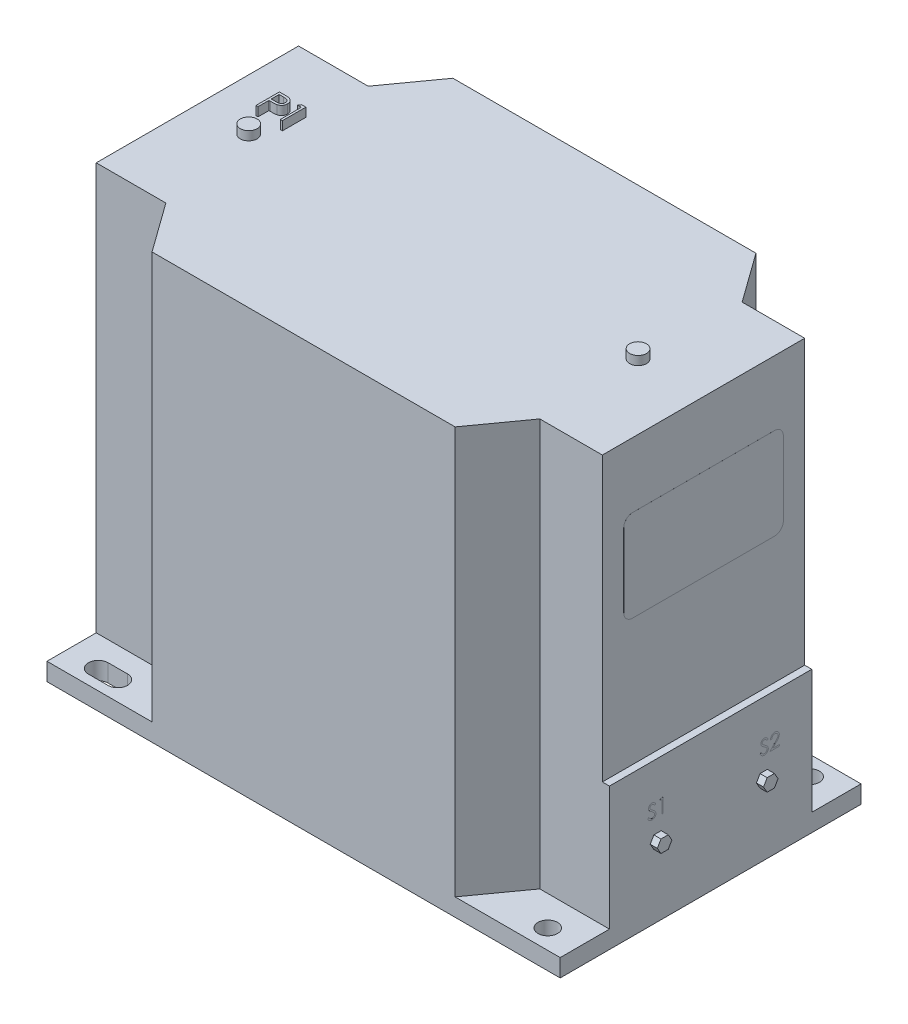
SolidWorks part; units mm, degrees
ref_plane "Alzado" through (0, 0, 0) normal (0, 0, 1) x (1, 0, 0)
ref_plane "Planta" through (0, 0, 0) normal (0, 1, 0) x (1, 0, 0)
ref_plane "Vista lateral" through (0, 0, 0) normal (1, 0, 0) x (0, 0, -1)
sketch "Croquis1" plane through (0, 0, 0) normal (0, 1, 0) x (1, 0, 0)
  line L1 (-145, 85) -> (145, 85)
  line L2 (-145, 85) -> (-145, -85)
  line L3 (-145, -85) -> (145, -85)
  line L4 (145, 85) -> (145, -85)
  line L5 (-145, 85) -> (145, -85) construction
  line L6 (-145, -85) -> (145, 85) construction
  point P0 (0, 0)
  dimension "D1" = 290
  dimension "D2" = 170
extrude "Saliente-Extruir1" add sketch "Croquis1" along normal blind 240
sketch "Croquis2" plane through (0, 240, 0) normal (0, 1, 0) x (1, 0, 0)
  line L0 (0, 0) -> (145, 0) construction
  line L1 (145, -85) -> (145, 85) construction
  line L2 (0, 0) -> (0, 85) construction
  line L3 (145, 85) -> (-145, 85) construction
  line L4 (-127, 74) -> (-116, 74) construction
  line L5 (-127, 79.5) -> (-116, 79.5)
  line L6 (-127, 68.5) -> (-116, 68.5)
  line L7 (-127, -74) -> (-116, -74) construction
  line L8 (-127, -79.5) -> (-116, -79.5)
  line L9 (-127, -68.5) -> (-116, -68.5)
  line L10 (-145, 57.1591) -> (-105.6531, 57.1591)
  line L11 (-145, 85) -> (-145, -85) construction
  line L12 (-105.6531, 57.1591) -> (-85.6261, 85)
  line L13 (145, 57.1591) -> (105.6531, 57.1591)
  line L14 (105.6531, 57.1591) -> (85.6261, 85)
  line L15 (145, -57.1591) -> (105.6531, -57.1591)
  line L16 (105.6531, -57.1591) -> (85.6261, -85)
  line L17 (-105.6531, -57.1591) -> (-85.6261, -85)
  line L18 (-145, -57.1591) -> (-105.6531, -57.1591)
  circle A0 centre (127, 74) radius 5.5
  circle A1 centre (127, -74) radius 5.5
  arc A2 (-127, 79.5) -> (-127, 68.5) centre (-127, 74) ccw
  arc A3 (-116, 68.5) -> (-116, 79.5) centre (-116, 74) ccw
  arc A4 (-127, -79.5) -> (-127, -68.5) centre (-127, -74) cw
  arc A5 (-116, -68.5) -> (-116, -79.5) centre (-116, -74) cw
  point P14 (-121.5, 74)
  point P22 (-121.5, -74)
  line M9 (145, -85) -> (145, 85)
  line M10 (145, 85) -> (-145, 85)
  line M11 (-145, 85) -> (-145, -85)
  line M12 (-145, -85) -> (145, -85)
  dimension "D1" = 11
  dimension "D2" = 74
  dimension "D3" = 127
  dimension "D4" = 11
  dimension "D5" = 254
  dimension "D6" = 11
extrude "Cortar-Extruir1" cut sketch "Croquis2" against normal blind 230 contours L18 L17 L9 A5 L8 A4 M11 M12 | L10 L12 A3 L6 A2 L5 M10 M11 | L14 L13 A0 M9 M10 | L15 L16 A1 M12 M9
sketch "Croquis3" plane through (0, 240, 0) normal (0, 1, 0) x (1, 0, 0)
  line L0 (-127, 74) -> (-116, 74) construction
  line L1 (-127, 79.5) -> (-116, 79.5)
  line L2 (-127, 68.5) -> (-116, 68.5)
  line L3 (-127, -74) -> (-116, -74) construction
  line L4 (-127, -68.4262) -> (-116, -68.4262)
  line L5 (-127, -79.5738) -> (-116, -79.5738)
  arc A0 (-127, 79.5) -> (-127, 68.5) centre (-127, 74) ccw
  arc A1 (-116, 68.5) -> (-116, 79.5) centre (-116, 74) ccw
  arc A2 (-127, -68.4262) -> (-127, -79.5738) centre (-127, -74) ccw
  arc A3 (-116, -79.5738) -> (-116, -68.4262) centre (-116, -74) ccw
  circle A4 centre (127, 74) radius 5.5
  circle A5 centre (127, -74) radius 5.5
  point P4 (-121.5, 74)
  point P9 (-121.5, -74)
  dimension "D2" = 11
  dimension "D1" = 11
extrude "Cortar-Extruir3" cut sketch "Croquis3" against normal blind 309
sketch "Croquis4" plane through (145, 0, 0) normal (1, 0, 0) x (0, 0, -1)
  line L0 (-57.1591, 0) -> (-57.1591, 80)
  line L1 (-85, 0) -> (85, 0) construction
  line L2 (-57.1591, 10) -> (-57.1591, 240) construction
  line L3 (-57.1591, 80) -> (57.1591, 80)
  line L4 (57.1591, 10) -> (57.1591, 240) construction
  line L5 (57.1591, 80) -> (57.1591, 0)
  line L6 (57.1591, 0) -> (-57.1591, 0)
  line L7 (-57.1591, 240) -> (-57.1591, 80)
  line L8 (-57.1591, 240) -> (57.1591, 240)
  line L11 (57.1591, 240) -> (57.1591, 80)
  line M2 (57.1591, 10) -> (57.1591, 240)
  line M3 (57.1591, 240) -> (-57.1591, 240)
  line M4 (-57.1591, 240) -> (-57.1591, 10)
  dimension "D1" = 80
extrude "Cortar-Extruir4" cut sketch "Croquis4" against normal blind 4 contours L3 M4 M2 M3
sketch "Croquis5" plane through (-145, 0, 0) normal (-1, 0, 0) x (0, 0, 1)
  line L1 (43.4139, 29.4196) -> (40.9893, 33.619)
  line L2 (40.9893, 33.619) -> (36.1403, 33.619)
  line L3 (36.1403, 33.619) -> (33.7158, 29.4196)
  line L4 (33.7158, 29.4196) -> (36.1403, 25.2202)
  line L5 (36.1403, 25.2202) -> (40.9893, 25.2202)
  line L6 (40.9893, 25.2202) -> (43.4139, 29.4196)
  circle A0 centre (38.5648, 29.4196) radius 4.1994 construction
extrude "Saliente-Extruir2" add sketch "Croquis5" along normal blind 4
sketch "Croquis6" plane through (-145, 0, 0) normal (-1, 0, 0) x (0, 0, 1)
  line L0 (43.4139, 29.4196) -> (33.7158, 29.4196) construction
  line L1 (33.7158, 29.4196) -> (38.5648, 29.4196) construction
  line L2 (38.5648, 29.4196) -> (38.5648, 74.3859) construction
  line L4 (43.4139, 74.3859) -> (40.9893, 78.5853)
  line L5 (40.9893, 78.5853) -> (36.1403, 78.5853)
  line L6 (36.1403, 78.5853) -> (33.7158, 74.3859)
  line L7 (33.7158, 74.3859) -> (36.1403, 70.1865)
  line L8 (36.1403, 70.1865) -> (40.9893, 70.1865)
  line L9 (40.9893, 70.1865) -> (43.4139, 74.3859)
  circle A0 centre (38.5648, 74.3859) radius 4.1994 construction
extrude "Saliente-Extruir3" add sketch "Croquis6" along normal blind 4
sketch "Croquis7" plane through (145, 0, 0) normal (1, 0, 0) x (0, 0, -1)
  line L0 (0, 0) -> (0, 80) construction
  line L1 (-85, 0) -> (85, 0) construction
  line L2 (-57.1591, 80) -> (57.1591, 80) construction
  line L3 (0, 40) -> (30, 40) construction
  line L4 (-27.9449, 36.4404) -> (-32.0551, 36.4404)
  line L5 (34.1103, 40) -> (32.0551, 43.5596)
  line L6 (32.0551, 43.5596) -> (27.9449, 43.5596)
  line L7 (27.9449, 43.5596) -> (25.8897, 40)
  line L8 (25.8897, 40) -> (27.9449, 36.4404)
  line L9 (27.9449, 36.4404) -> (32.0551, 36.4404)
  line L10 (32.0551, 36.4404) -> (34.1103, 40)
  line L11 (-32.0551, 36.4404) -> (-34.1103, 40)
  line L12 (-34.1103, 40) -> (-32.0551, 43.5596)
  line L13 (-32.0551, 43.5596) -> (-27.9449, 43.5596)
  line L14 (-27.9449, 43.5596) -> (-25.8897, 40)
  line L15 (-25.8897, 40) -> (-27.9449, 36.4404)
  circle A0 centre (30, 40) radius 3.5596 construction
  dimension "D1" = 30
extrude "Saliente-Extruir5" add sketch "Croquis7" along normal blind 4
sketch "Croquis8" plane through (145, 0, 0) normal (1, 0, 0) x (0, 0, -1)
  text T0 "              \r\n\r\n       S1                 S2" font "Century Gothic" height in points 30
extrude "Saliente-Extruir6" add sketch "Croquis8" along normal blind 0.01
sketch "Croquis9" plane through (-145, 0, 0) normal (-1, 0, 0) x (0, 0, 1)
  text T0 "\r\n\r\n\r\n\r\n\r\n\r\n                P2\r\n                                                  \r\n" font "Century Gothic" height in points 50
extrude "Saliente-Extruir7" add sketch "Croquis9" along normal blind 0.01
sketch "Croquis10" plane through (141, 0, 0) normal (1, 0, 0) x (0, 0, -1)
  line L1 (-40.0867, 203.3344) -> (40.0867, 203.3344)
  line L2 (-45.0867, 198.3344) -> (-45.0867, 156.662)
  line L3 (-40.0867, 151.662) -> (40.0867, 151.662)
  line L4 (45.0867, 198.3344) -> (45.0867, 156.662)
  line L5 (-45.0867, 203.3344) -> (45.0867, 151.662) construction
  line L6 (-45.0867, 151.662) -> (45.0867, 203.3344) construction
  arc A0 (40.0867, 203.3344) -> (45.0867, 198.3344) centre (40.0867, 198.3344) cw
  arc A1 (40.0867, 151.662) -> (45.0867, 156.662) centre (40.0867, 156.662) ccw
  arc A2 (-45.0867, 156.662) -> (-40.0867, 151.662) centre (-40.0867, 156.662) ccw
  arc A3 (-40.0867, 203.3344) -> (-45.0867, 198.3344) centre (-40.0867, 198.3344) ccw
  point P0 (0, 177.4982)
  dimension "D1" = 5
extrude "Saliente-Extruir8" add sketch "Croquis10" along normal blind 0.01
sketch "Croquis11" plane through (0, 240, 0) normal (0, 1, 0) x (1, 0, 0)
  line L0 (-145, 0) -> (141, 0) construction
  line L1 (141, -57.1591) -> (141, 57.1591) construction
  line L2 (-145, 57.1591) -> (-145, -57.1591) construction
  circle A0 centre (-116, 0) radius 4.75
  circle A1 centre (104, 0) radius 4.75
  text T0 " \r\n\r\n    P1" font "Century Gothic" height in points 50
  dimension "D1" = 9.5
  dimension "D2" = 9.5
  dimension "D3" = 110
  dimension "D4" = 110
extrude "Saliente-Extruir9" add sketch "Croquis11" along normal blind 5
sketch "Croquis12" plane through (-145, 0, 0) normal (-1, 0, 0) x (0, 0, 1)
  line L1 (5.8053, 35.8489) -> (25.2829, 35.8489)
  line L2 (5.8053, 35.8489) -> (5.8053, 33.9011)
  line L3 (5.8053, 33.9011) -> (25.2829, 33.9011)
  line L4 (25.2829, 35.8489) -> (25.2829, 33.9011)
  line L5 (5.8053, 35.8489) -> (25.2829, 33.9011) construction
  line L6 (5.8053, 33.9011) -> (25.2829, 35.8489) construction
  line L7 (8.1682, 33.1073) -> (22.92, 33.1073)
  line L8 (8.1682, 33.1073) -> (8.1682, 31.2782)
  line L9 (8.1682, 31.2782) -> (22.92, 31.2782)
  line L10 (22.92, 33.1073) -> (22.92, 31.2782)
  line L11 (8.1682, 33.1073) -> (22.92, 31.2782) construction
  line L12 (8.1682, 31.2782) -> (22.92, 33.1073) construction
  line L13 (12.9314, 26.6468) -> (18.1568, 26.6468)
  line L14 (12.9314, 26.6468) -> (12.9314, 25.4007)
  line L15 (12.9314, 25.4007) -> (18.1568, 25.4007)
  line L16 (18.1568, 26.6468) -> (18.1568, 25.4007)
  line L17 (12.9314, 26.6468) -> (18.1568, 25.4007) construction
  line L18 (12.9314, 25.4007) -> (18.1568, 26.6468) construction
  line L19 (14.5892, 59.0604) -> (16.499, 59.0604)
  line L20 (14.5892, 59.0604) -> (14.5892, 36.572)
  line L21 (14.5892, 36.572) -> (16.499, 36.572)
  line L22 (16.499, 59.0604) -> (16.499, 36.572)
  line L23 (14.5892, 59.0604) -> (16.499, 36.572) construction
  line L24 (14.5892, 36.572) -> (16.499, 59.0604) construction
  line L25 (10.525, 30.3038) -> (20.5632, 30.3038)
  line L26 (10.525, 30.3038) -> (10.525, 28.6247)
  line L27 (10.525, 28.6247) -> (20.5632, 28.6247)
  line L28 (20.5632, 30.3038) -> (20.5632, 28.6247)
  line L29 (10.525, 30.3038) -> (20.5632, 28.6247) construction
  line L30 (10.525, 28.6247) -> (20.5632, 30.3038) construction
  point P0 (15.5441, 34.875)
  point P5 (15.5441, 26.0237)
  point P6 (15.5441, 32.1928)
  point P15 (15.5441, 47.8162)
  point P20 (17.1875, 23.692)
  point P21 (15.5441, 26.0237)
  point P22 (15.5441, 29.4643)
extrude "Saliente-Extruir10" add sketch "Croquis12" along normal blind 0.1
